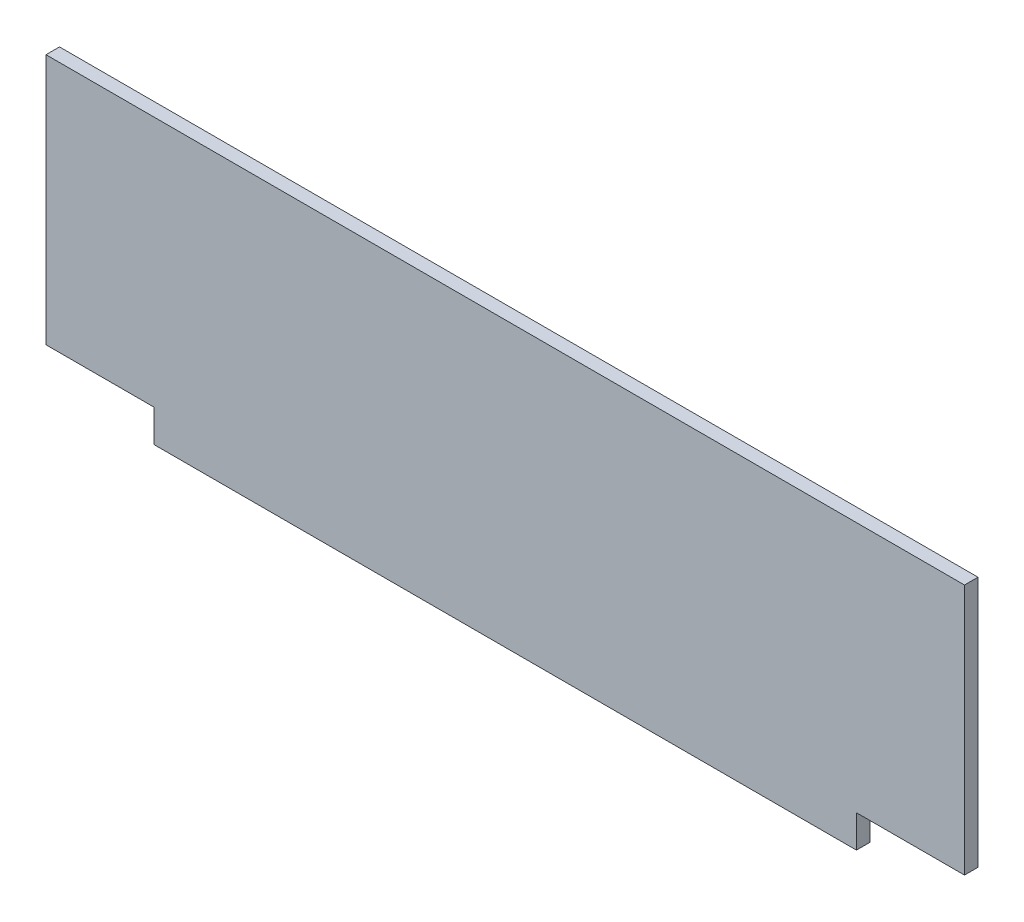
SolidWorks part; units mm, degrees
ref_plane "Plan de face" through (0, 0, 0) normal (0, 0, 1) x (1, 0, 0)
ref_plane "Plan de dessus" through (0, 0, 0) normal (0, 1, 0) x (1, 0, 0)
ref_plane "Plan de droite" through (0, 0, 0) normal (1, 0, 0) x (0, 0, -1)
sketch "Esquisse1" plane through (0, 0, 0) normal (0, 0, 1) x (1, 0, 0)
  line L1 (-340, 105) -> (340, 105)
  line L2 (-340, 105) -> (-340, -105)
  line L3 (-340, -105) -> (340, -105)
  line L4 (340, 105) -> (340, -105)
  dimension "D1" = 680
  dimension "D2" = 210
  dimension "D3" = 105
  dimension "D4" = 340
extrude "Boss.-Extru.1" add sketch "Esquisse1" along normal blind 10
sketch "Esquisse2" plane through (0, 0, 10) normal (0, 0, 1) x (1, 0, 0)
  line L1 (-340, -105) -> (-260, -105)
  line L2 (-340, -105) -> (-340, -81)
  line L3 (-340, -81) -> (-260, -81)
  line L4 (-260, -105) -> (-260, -81)
  line L5 (340, -105) -> (260, -105)
  line L6 (340, -105) -> (340, -81)
  line L7 (340, -81) -> (260, -81)
  line L8 (260, -105) -> (260, -81)
  dimension "D1" = 80
  dimension "D2" = 80
  dimension "D3" = 24
  dimension "D4" = 24
extrude "Enlèv. mat.-Extru.1" cut sketch "Esquisse2" against normal through all
